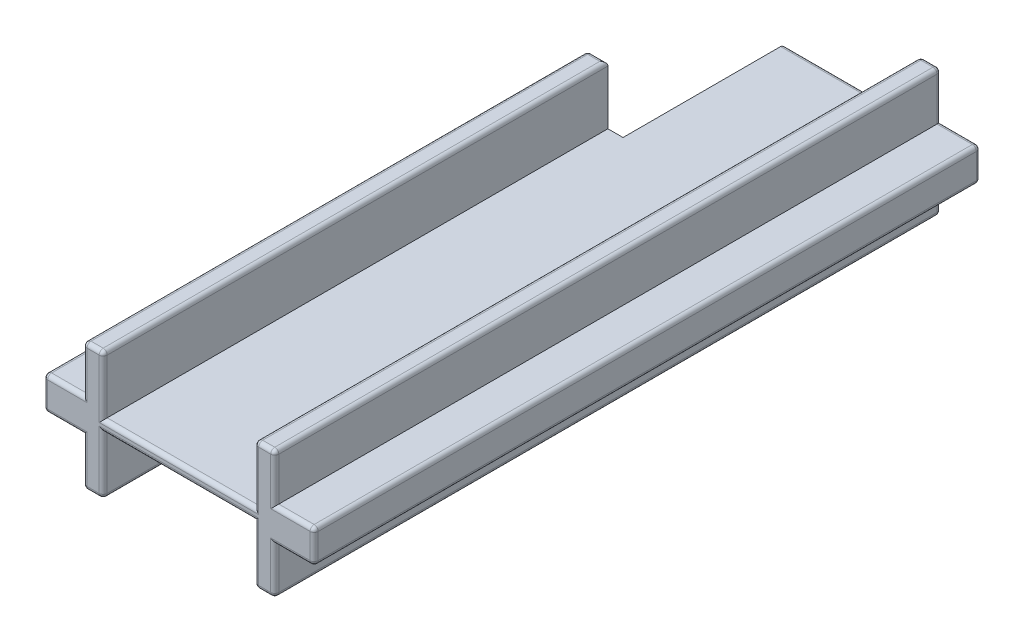
SolidWorks part; units mm, degrees
ref_plane "Ebene vorne" through (0, 0, 0) normal (0, 0, 1) x (1, 0, 0)
ref_plane "Ebene oben" through (0, 0, 0) normal (0, 1, 0) x (1, 0, 0)
ref_plane "Ebene rechts" through (0, 0, 0) normal (1, 0, 0) x (0, 0, -1)
sketch "Skizze1" plane through (0, 0, 0) normal (0, 0, 1) x (1, 0, 0)
  line L0 (-4.75, 0.825) -> (-6.7, 0.825)
  line L1 (6.7, -0.825) -> (4.75, -0.825)
  line L2 (6.7, -0.825) -> (6.7, 0.825)
  line L3 (6.7, 0.825) -> (4.75, 0.825)
  line L4 (-6.7, -0.825) -> (-6.7, 0.825)
  line L5 (6.7, -0.825) -> (-6.7, 0.825) construction
  line L6 (6.7, 0.825) -> (-6.7, -0.825) construction
  line L7 (-4.75, -3.165) -> (-3.75, -3.165)
  line L8 (-4.75, -3.165) -> (-4.75, -0.825)
  line L9 (-4.75, 3.165) -> (-3.75, 3.165)
  line L10 (-3.75, -3.165) -> (-3.75, -0.825)
  line L11 (-4.75, -3.165) -> (-3.75, 3.165) construction
  line L12 (-4.75, 3.165) -> (-3.75, -3.165) construction
  line L13 (4.75, -3.165) -> (3.75, -3.165)
  line L14 (4.75, -3.165) -> (4.75, -0.825)
  line L15 (4.75, 3.165) -> (3.75, 3.165)
  line L16 (3.75, -3.165) -> (3.75, -0.825)
  line L17 (4.75, -3.165) -> (3.75, 3.165) construction
  line L18 (4.75, 3.165) -> (3.75, -3.165) construction
  line L19 (-4.75, -0.825) -> (-6.7, -0.825)
  line L20 (-4.75, 0.825) -> (-4.75, 3.165)
  line L21 (-3.75, 0.825) -> (-3.75, 3.165)
  line L22 (3.75, -0.825) -> (-3.75, -0.825)
  line L23 (3.75, 0.825) -> (3.75, 3.165)
  line L24 (4.75, 0.825) -> (4.75, 3.165)
  line L25 (3.75, 0.825) -> (-3.75, 0.825)
  point P0 (0, 0)
  point P5 (-4.25, 0)
  point P11 (4.25, 0)
  dimension "D1" = 1.65
  dimension "D2" = 2.34
  dimension "D3" = 13.4
  dimension "D4" = 9.5
  dimension "D5" = 1
  dimension "D6" = 4.75
extrude "Aufsatz-Linear austragen1" add sketch "Skizze1" along normal blind 25
sketch "Skizze2" plane through (0, 0, 0) normal (0, 0, -1) x (-1, 0, 0)
  line L0 (-3.75, 0.825) -> (3.75, 0.825) construction
  line L1 (3, -0.825) -> (-3, -0.825)
  line L2 (3, -0.825) -> (3, 0.825)
  line L3 (3, 0.825) -> (-3, 0.825)
  line L4 (-3, -0.825) -> (-3, 0.825)
  line L5 (3, -0.825) -> (-3, 0.825) construction
  line L6 (3, 0.825) -> (-3, -0.825) construction
  point P0 (0, 0)
  dimension "D1" = 6
extrude "Aufsatz-Linear austragen2" add sketch "Skizze2" along normal blind 8
sketch "Skizze3" plane through (0, 0, 25) normal (0, 0, 1) x (1, 0, 0)
  line L1 (-3.75, -0.825) -> (3.75, -0.825)
  line L2 (-3.75, -0.825) -> (-3.75, -0.275)
  line L3 (-3.75, -0.275) -> (3.75, -0.275)
  line L4 (3.75, -0.825) -> (3.75, -0.275)
  line L5 (3.75, 0.825) -> (-3.75, 0.825)
  line L6 (3.75, 0.825) -> (3.75, 0.275)
  line L7 (3.75, 0.275) -> (-3.75, 0.275)
  line L8 (-3.75, 0.825) -> (-3.75, 0.275)
  dimension "D1" = 0.55
  dimension "D2" = 0.275
extrude "Schnitt-Linear austragen1" cut sketch "Skizze3" against normal through all
sketch "Skizze4" plane through (0, 0, 0) normal (0, 0, -1) x (-1, 0, 0)
  line L0 (-3.75, -3.165) -> (-4.75, -3.165)
  line L1 (-4.75, -3.165) -> (-4.75, -0.825)
  line L2 (-4.75, -0.825) -> (-6.7, -0.825)
  line L3 (-4.75, -0.825) -> (-6.7, -0.825) construction
  line L4 (-6.7, -0.825) -> (-6.7, 0.825) construction
  line L5 (-6.7, -0.825) -> (-6.7, 0.825)
  line L6 (-6.7, 0.825) -> (-4.75, 0.825)
  line L7 (-4.75, 0.825) -> (-4.75, 3.165)
  line L8 (-4.75, 3.165) -> (-3.75, 3.165)
  line L9 (-3.75, 3.165) -> (-3.75, 0.275)
  line L10 (-3.75, 0.275) -> (-3, 0.275)
  line L11 (-3, 0.275) -> (-3, -0.275)
  line L12 (-3, -0.275) -> (-3.75, -0.275)
  line L13 (-3.75, -0.275) -> (-3.75, -3.165)
extrude "Aufsatz-Linear austragen3" add sketch "Skizze4" along normal up to surface (8 mm away) up to face at (0, 0, -8)
fillet "Verrundung1" radius 0.2 51 edges at (-5.725, 0.825, 25) (-4.75, 1.995, 25) (-3.75, 1.72, 25) (3.75, 1.72, 25) (4.75, 1.995, 25) (5.725, 0.825, 25) (5.725, -0.825, 25) (4.75, -1.995, 25) (3.75, -1.72, 25) (-3.75, -1.72, 25) (-4.75, -1.995, 25) (-5.725, -0.825, 25) (-3, 0, -8) (-6.7, 0.825, 12.5) (-6.7, 0, 25) (-6.7, -0.825, 12.5) (-6.7, 0, 0) (6.7, -0.825, 8.5) (6.7, 0, 25) (6.7, 0.825, 8.5) (-4.75, -3.165, 12.5) (-3.75, -3.165, 12.5) (-4.25, -3.165, 0) (3.75, -3.165, 8.5) (4.75, -3.165, 8.5) (-3.75, 3.165, 12.5) (-4.75, 3.165, 12.5) (-4.25, 3.165, 0) (4.75, 3.165, 8.5) (3.75, 3.165, 8.5) (-4.75, 1.995, 0) (-4.75, -1.995, 0) (-5.725, 0.825, 0) (-5.725, -0.825, 0) (-4.25, -3.165, 25) (4.25, -3.165, 25) (-4.25, 3.165, 25) (4.25, 3.165, 25) (0, 0.275, 25) (0, -0.275, 25) (0.375, 0.275, -8) (0.375, -0.275, -8) (3.75, -1.72, -8) (4.75, -1.995, -8) (5.725, -0.825, -8) (5.725, 0.825, -8) (4.75, 1.995, -8) (3.75, 1.72, -8) (6.7, 0, -8) (4.25, -3.165, -8) (4.25, 3.165, -8)
